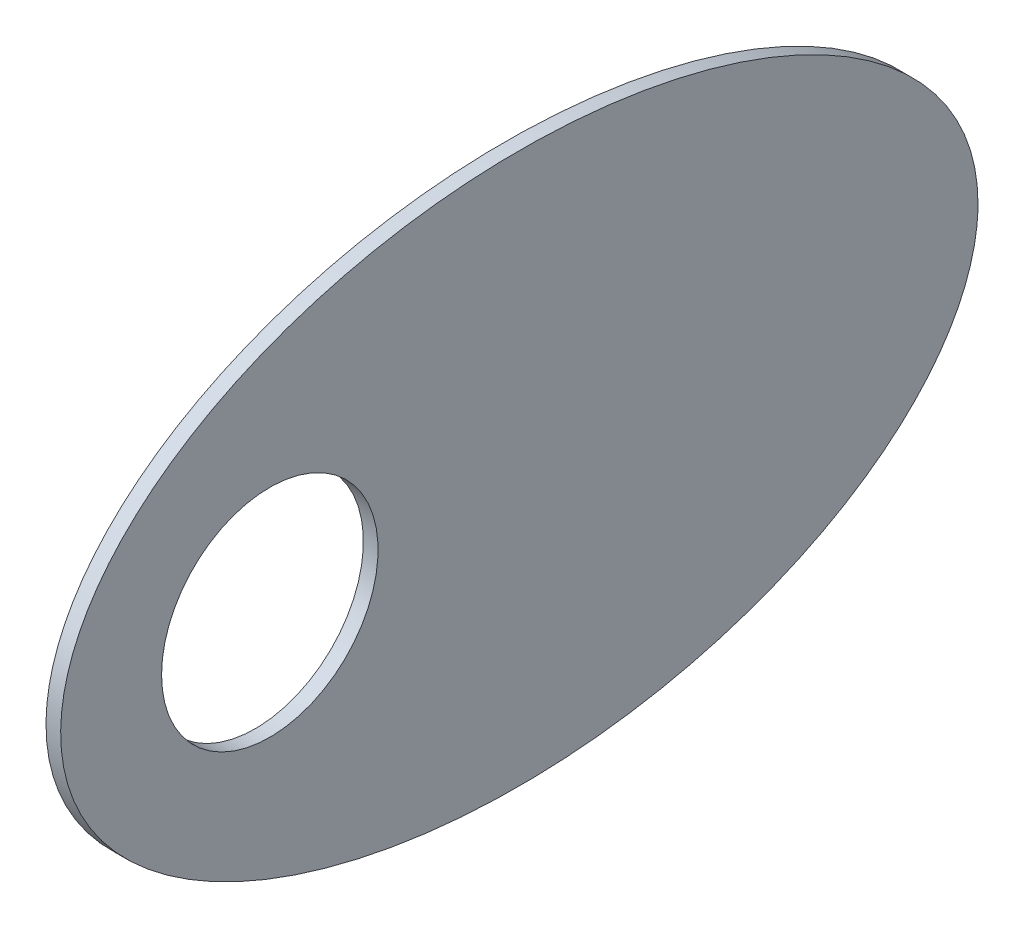
SolidWorks part; units mm, degrees
ref_plane "Front Plane" through (0, 0, 0) normal (0, 0, 1) x (1, 0, 0)
ref_plane "Top Plane" through (0, 0, 0) normal (0, 1, 0) x (1, 0, 0)
ref_plane "Right Plane" through (0, 0, 0) normal (1, 0, 0) x (0, 0, -1)
sketch "Sketch1" plane through (0, 0, 0) normal (1, 0, 0) x (0, 0, -1)
  ellipse E0 centre (0, 0) end of major axis (125, 0) minor radius 75
  dimension "D1" = 150
  dimension "D2" = 250
extrude "Boss-Extrude1" add sketch "Sketch1" along normal blind 4
sketch "Sketch2" plane through (0, 0, 0) normal (-1, 0, 0) x (0, 0, 1)
  circle A0 centre (68, 0) radius 29.5
  dimension "D1" = 59
  dimension "D2" = 68
extrude "Cut-Extrude1" cut sketch "Sketch2" against normal through all
